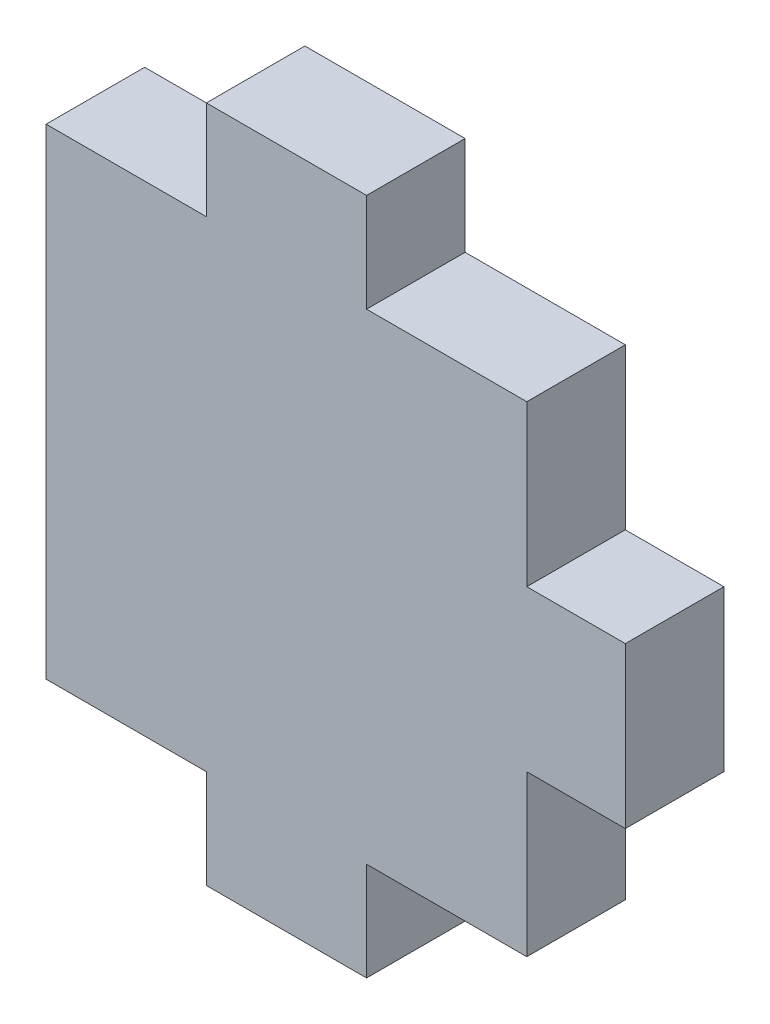
SolidWorks part; units mm, degrees
ref_plane "Front Plane" through (0, 0, 0) normal (0, 0, 1) x (1, 0, 0)
ref_plane "Top Plane" through (0, 0, 0) normal (0, 1, 0) x (1, 0, 0)
ref_plane "Right Plane" through (0, 0, 0) normal (1, 0, 0) x (0, 0, -1)
sketch "Sketch1" plane through (0, 0, 0) normal (0, 0, 1) x (1, 0, 0)
  line L0 (10.7861, 17.5054) -> (19.2528, 17.5054)
  line L1 (-6.1472, 17.5054) -> (2.3195, 17.5054)
  line L2 (-6.1472, 17.5054) -> (-6.1472, -7.8946)
  line L3 (-6.1472, -7.8946) -> (2.3195, -7.8946)
  line L4 (19.2528, 17.5054) -> (19.2528, 9.0387)
  line L5 (19.2528, 0.572) -> (19.2528, -7.8946)
  line L6 (2.3195, 17.5054) -> (2.3195, 22.7124)
  line L7 (2.3195, 22.7124) -> (10.7861, 22.7124)
  line L8 (10.7861, 17.5054) -> (10.7861, 22.7124)
  line L9 (19.2528, 9.0387) -> (24.4598, 9.0387)
  line L10 (10.7861, -7.8946) -> (19.2528, -7.8946)
  line L11 (19.2528, 0.572) -> (24.4598, 0.572)
  line L12 (24.4598, 9.0387) -> (24.4598, 0.572)
  line L14 (2.3195, -7.8946) -> (2.3195, -13.1016)
  line L15 (2.3195, -13.1016) -> (10.7861, -13.1016)
  line L16 (10.7861, -7.8946) -> (10.7861, -13.1016)
  dimension "D1" = 25.4
  dimension "D2" = 25.4
  dimension "D3" = 5.207
extrude "Boss-Extrude1" add sketch "Sketch1" along normal blind 5.207
equation "\"mat\" = \"mat2@jaws.assembly\""
equation "\"D3@Sketch1\"= \"mat\""
equation "\"D1@Boss-Extrude1\"= \"mat\""
